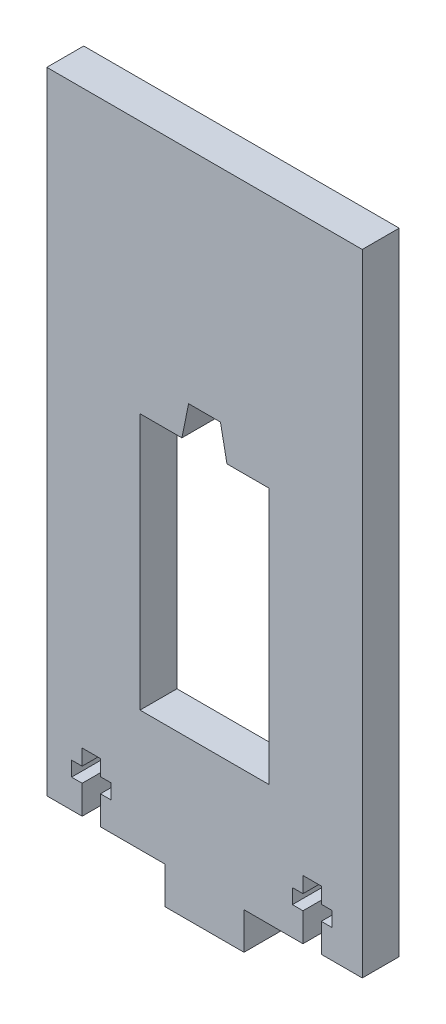
SolidWorks part; units mm, degrees
ref_plane "Front Plane" through (0, 0, 0) normal (0, 0, 1) x (1, 0, 0)
ref_plane "Top Plane" through (0, 0, 0) normal (0, 1, 0) x (1, 0, 0)
ref_plane "Right Plane" through (0, 0, 0) normal (1, 0, 0) x (0, 0, -1)
sketch "Sketch2" plane through (0, 0, 0) normal (0, 0, 1) x (1, 0, 0)
  line L0 (-25.4, 101.6) -> (-25.4, -11.7606) construction
  line L1 (0, 0) -> (0, 101.6)
  line L2 (0, 0) -> (-19.05, 0)
  line L3 (-50.8, 0) -> (-50.8, 101.6)
  line L4 (0, 101.6) -> (-50.8, 101.6)
  line L5 (-31.75, 0) -> (-31.75, -5.9436)
  line L6 (-19.05, -5.9436) -> (-19.05, 0)
  line L7 (-31.75, -5.9436) -> (-19.05, -5.9436)
  line L8 (-31.75, 0) -> (-50.8, 0)
  point P13 (-25.4, -5.9436)
  dimension "D1" = 101.6
  dimension "D2" = 50.8
  dimension "D3" = 5.9436
  dimension "D4" = 12.7
extrude "Boss-Extrude1" add sketch "Sketch2" along normal blind 5.9436
sketch "Sketch3" plane through (0, 0, 5.9436) normal (0, 0, 1) x (1, 0, 0)
  line L0 (-25.4, 101.6) -> (-25.4, -0.683) construction
  line L1 (-27.9655, 66.1106) -> (-22.8345, 66.1106)
  line L2 (-22.8345, 66.1106) -> (-21.7927, 60.7998)
  line L3 (0, 101.6) -> (-50.8, 101.6) construction
  line L5 (-35.7869, 60.7998) -> (-35.7869, 19.4674)
  line L6 (-35.7869, 19.4674) -> (-15.0131, 19.4674)
  line L7 (-15.0131, 60.7998) -> (-15.0131, 19.4674)
  line L8 (-27.9655, 66.1106) -> (-29.0458, 60.8)
  line L9 (-21.7927, 60.7998) -> (-15.0131, 60.7998)
  line L10 (-35.7869, 60.7998) -> (-29.0458, 60.8)
  line L11 (-19.05, 0) -> (0, 0) construction
  point P2 (-25.4, 19.4674)
  point P15 (-25.4, 66.1106)
  dimension "D1" = 41.3324
  dimension "D2" = 20.7738
  dimension "D3" = 19.4674
extrude "Cut-Extrude1" cut sketch "Sketch3" against normal through all
sketch "Sketch4" plane through (0, 0, 5.9436) normal (0, 0, 1) x (1, 0, 0)
  line L1 (-9.5502, -0.0003) -> (-9.5502, 4.6038)
  line L27 (-9.5502, 4.6038) -> (-11.252, 4.6038)
  line L28 (-11.252, 4.6038) -> (-11.252, 6.985)
  line L29 (-11.252, 6.985) -> (-9.5502, 6.985)
  line L30 (-9.5502, 6.985) -> (-9.5502, 9.525)
  line L31 (-9.5502, 9.525) -> (-6.6038, 9.525)
  line L32 (-6.6038, 9.525) -> (-6.6038, 6.985)
  line L33 (-6.6038, 6.985) -> (-4.902, 6.985)
  line L34 (-4.902, 6.985) -> (-4.902, 4.6037)
  line L35 (-4.902, 4.6037) -> (-6.6038, 4.6037)
  line L36 (-6.6038, 4.6037) -> (-6.6038, -0.0003)
  line L39 (-25.857, -5.9436) -> (-25.857, 15.3212) construction
  line L41 (-46.812, 4.6037) -> (-45.1102, 4.6037)
  line L42 (-46.812, 6.985) -> (-46.812, 4.6037)
  line L43 (-45.1102, 6.985) -> (-46.812, 6.985)
  line L44 (-45.1102, 4.6037) -> (-45.1102, -0.0003)
  line L45 (-45.1102, 9.525) -> (-45.1102, 6.985)
  line L46 (-42.1638, 9.525) -> (-45.1102, 9.525)
  line L47 (-42.1638, 6.985) -> (-42.1638, 9.525)
  line L48 (-40.462, 6.985) -> (-42.1638, 6.985)
  line L49 (-40.462, 4.6038) -> (-40.462, 6.985)
  line L50 (-42.1638, 4.6038) -> (-40.462, 4.6038)
  line L51 (-42.1638, -0.0003) -> (-42.1638, 4.6038)
  line L52 (-6.6038, -0.0003) -> (-9.5502, -0.0003)
  line L53 (-42.1638, -0.0003) -> (-45.1102, -0.0003)
extrude "Cut-Extrude2" cut sketch "Sketch4" against normal through all
